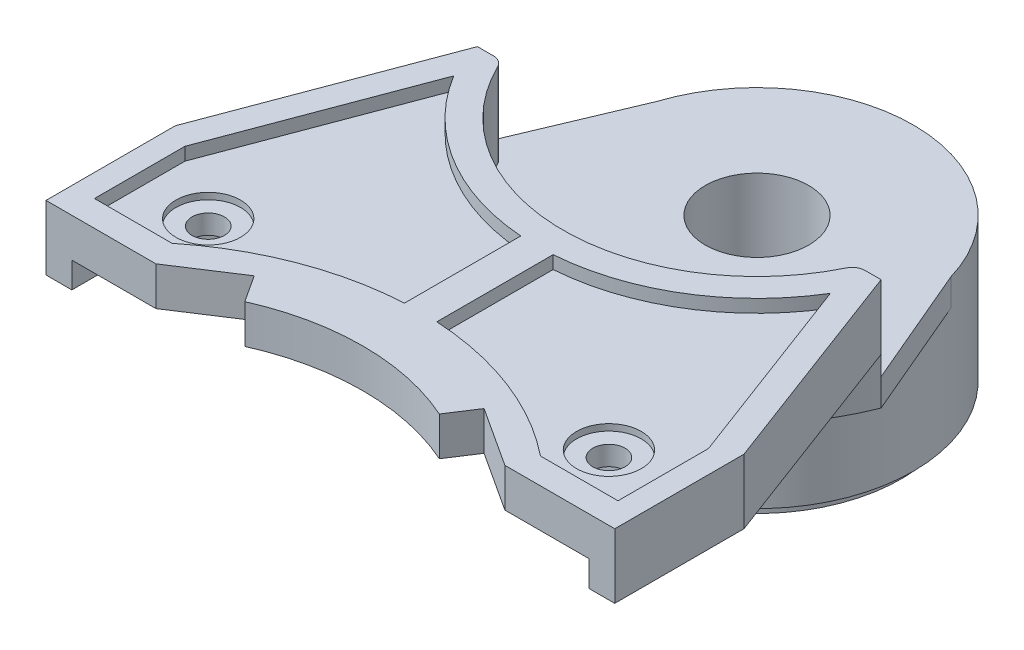
SolidWorks part; units mm, degrees
material "ABS"
ref_plane "Front Plane" through (0, 0, 0) normal (0, 0, 1) x (1, 0, 0)
ref_plane "Top Plane" through (0, 0, 0) normal (0, 1, 0) x (1, 0, 0)
ref_plane "Right Plane" through (0, 0, 0) normal (1, 0, 0) x (0, 0, -1)
sketch "Sketch1" plane through (0, 0, 0) normal (0, 1, 0) x (1, 0, 0)
  line L0 (-22, -33.0049) -> (-13.5, -33.0049)
  line L1 (-13.5, -33.0049) -> (13.5, -33.0049) construction
  line L2 (-22, -33.0049) -> (-22, -23.0049)
  line L3 (0, -30.5) -> (0, 12.5)
  line L4 (-13.5, -33.0049) -> (-8.8902, -30.0049)
  line L5 (0, -2.75) -> (0, 2.75) construction
  line L6 (-8.8902, -30.0049) -> (-7.5266, -32.1003)
  line L7 (-11.7009, 4.3977) -> (-22, -23.0049)
  line L8 (11.7009, 4.3977) -> (22, -23.0049)
  line L9 (8.8902, -30.0049) -> (7.5266, -32.1003)
  line L10 (13.5, -33.0049) -> (8.8902, -30.0049)
  line L11 (22, -33.0049) -> (22, -23.0049)
  line L12 (22, -33.0049) -> (13.5, -33.0049)
  arc A0 (11.7009, 4.3977) -> (-11.7009, 4.3977) centre (0, 0) ccw
  arc A2 (7.5266, -32.1003) -> (-7.5266, -32.1003) centre (0, -49) ccw
  point P5 (0, -33.0049)
  point P11 (0, -49)
  dimension "D1" = 25
  dimension "D5" = 18.5
  dimension "D2" = 8.5
  dimension "D3" = 5.5
  dimension "D4" = 10
  dimension "D6" = 13.5
  dimension "D7" = 2.5
  dimension "D8" = 90
  dimension "D9" = 3
  dimension "D11" = 49
extrude "Boss-Extrude1" add sketch "Sketch1" along normal blind 5 contours A2 L3 A0 L7 L2 L0 L4 L6 | A2 L9 L10 L12 L11 L8 A0 L3
sketch "Sketch3" plane through (0, 5, 0) normal (0, 1, 0) x (1, 0, 0)
  circle A0 centre (0, 0) radius 15
  dimension "D1" = 30
sketch "Sketch6" plane through (0, 5, 0) normal (0, 1, 0) x (1, 0, 0)
  line L0 (1.2511, -26.0226) -> (20.2511, -26.0226) construction
  line L1 (-1.2511, -17.0226) -> (-1.2511, -26.0226)
  line L2 (-1.2511, -26.0226) -> (-20.2511, -26.0226) construction
  line L3 (-20.2511, -24.0049) -> (-20.2511, -31.0049)
  line L4 (-22, -33.0049) -> (-13.5, -33.0049) construction
  line L5 (0, -2.75) -> (0, 2.75) construction
  line L6 (-20.2511, -31.0049) -> (-14.2511, -31.0049)
  line L7 (-20.2511, -24.0049) -> (-14.5704, -8.8904)
  line L8 (-11.7009, 4.3977) -> (-22, -23.0049) construction
  line L9 (20.2511, -24.0049) -> (14.5704, -8.8904)
  line L10 (20.2511, -31.0049) -> (14.2511, -31.0049)
  line L11 (20.2511, -24.0049) -> (20.2511, -31.0049)
  line L12 (1.2511, -17.0226) -> (1.2511, -26.0226)
  arc A0 (-14.5704, -8.8904) -> (-1.2511, -17.0226) centre (0, 0) ccw
  arc A1 (-1.2511, -26.0226) -> (-14.2511, -31.0049) centre (0, -48.7383) ccw
  arc A2 (1.2511, -26.0226) -> (14.2511, -31.0049) centre (0, -48.7383) cw
  arc A3 (14.5704, -8.8904) -> (1.2511, -17.0226) centre (0, 0) cw
  dimension "D10" = 360
  dimension "D8" = 22.7501
  dimension "D2" = 2.5023
  dimension "D3" = 9
  dimension "D4" = 19
  dimension "D5" = 7
  dimension "D6" = 2
  dimension "D7" = 6
sketch "Sketch7" plane through (0, 5, 0) normal (0, 1, 0) x (1, 0, 0)
  circle A0 centre (-15.5, -26.9549) radius 1.25
  circle A1 centre (15.5, -26.9549) radius 1.25
  dimension "D3" = 2.5
  dimension "D4" = 2.5
  dimension "D1" = 31
  dimension "D2" = 26.9549
sketch "Sketch8" plane through (0, 5, 0) normal (0, 1, 0) x (1, 0, 0)
  line L0 (-22, -33.0049) -> (-13.5, -33.0049) construction
  line L1 (0, -2.75) -> (0, 2.75) construction
  circle A0 centre (-15.5, -26.9549) radius 2.5
  circle A1 centre (15.5, -26.9549) radius 2.5
  dimension "D1" = 5
  dimension "D2" = 6.05
  dimension "D3" = 15.5
sketch "Sketch9" plane through (0, 0, 0) normal (0, -1, 0) x (1, 0, 0)
  line L0 (0, 30.5) -> (0, 18) construction
  line L1 (0, -2.75) -> (0, 2.75) construction
  line L2 (22, 33.0049) -> (22, 23.0049) construction
  line L3 (22, 33.0049) -> (13.5, 33.0049) construction
  line L4 (20, 33.0049) -> (20, 27.0049)
  line L5 (-20, 33.0049) -> (-20, 27.0049)
  line L7 (20, 33.0049) -> (-20, 33.0049)
  arc A3 (-20, 27.0049) -> (20, 27.0049) centre (0, 44.7125) ccw
  arc A6 (-7.5266, 32.1003) -> (7.5266, 32.1003) centre (0, 49) ccw construction
  dimension "D5" = 0
  dimension "D2" = 2
  dimension "D1" = 0
  dimension "D6" = 12.5
  dimension "D7" = 0
  dimension "D8" = 44.7125
extrude "Cut-Extrude6" cut sketch "Sketch9" against normal blind 2
sketch "Sketch11" plane through (0, 0, 0) normal (0, -1, 0) x (1, 0, 0)
  line L0 (-20, 33.0049) -> (-20, 23.0049) construction
  line L1 (-20, 23.0049) -> (-10.0731, -3.4072)
  line L2 (-11.7009, -4.3977) -> (-22, 23.0049) construction
  line L3 (-20, 23.0049) -> (-20, 25.5296)
  line L4 (0, -2.75) -> (0, 2.75) construction
  line L5 (20, 23.0049) -> (20, 25.5296)
  line L6 (20, 23.0049) -> (10.0731, -3.4072)
  arc A0 (-20, 25.5296) -> (20, 25.5296) centre (0, 44.7125) ccw
  arc A1 (-10.0731, -3.4072) -> (10.0731, -3.4072) centre (0, 0) ccw
  dimension "D1" = 27.7125
  dimension "D2" = 10
  dimension "D3" = 0
extrude "Cut-Extrude7" cut sketch "Sketch11" against normal blind 2
sketch "Sketch12" plane through (0, 5, 0) normal (0, -1, 0) x (1, 0, 0)
  circle A0 centre (0, 0) radius 16.7324
  dimension "D1" = 33.4649
extrude "Boss-Extrude3" add sketch "Sketch12" along normal blind 8.6
sketch "Sketch13" plane through (0, -3.6, 0) normal (0, -1, 0) x (1, 0, 0)
  circle A0 centre (0, 0) radius 10.4
  circle A1 centre (0, 0) radius 12.1
  dimension "D1" = 20.8
  dimension "D2" = 24.2
sketch "Sketch14" plane through (0, -3.6, 0) normal (0, -1, 0) x (1, 0, 0)
  circle A0 centre (0, 0) radius 6
  dimension "D1" = 12
extrude "Boss-Extrude4" add sketch "Sketch13" along normal blind 10
extrude "Boss-Extrude5" add sketch "Sketch14" along normal blind 10
sketch "Sketch15" plane through (0, -13.6, 0) normal (0, -1, 0) x (1, 0, 0)
  circle A0 centre (0, 0) radius 1.25
  dimension "D1" = 2.5
sketch "Sketch18" plane through (0, -13.6, 0) normal (0, 1, 0) x (1, 0, 0)
extrude "Cut-Extrude10" cut sketch "Sketch6" against normal blind 1
extrude "Cut-Extrude11" cut sketch "Sketch7" against normal through all
extrude "Cut-Extrude12" cut sketch "Sketch8" against normal blind 1.5
extrude "Cut-Extrude14" cut sketch "Sketch3" against normal blind 6.5
sketch "Sketch19" plane through (0, 5, 0) normal (0, 1, 0) x (1, 0, 0)
  line L0 (-15.6142, -6.0143) -> (15.6142, -6.0143)
  arc A0 (15.6142, -6.0143) -> (-15.6142, -6.0143) centre (0, 0) ccw
extrude "Cut-Extrude15" cut sketch "Sketch19" against normal blind 6.5
extrude "Cut-Extrude16" cut sketch "Sketch15" against normal blind 6.5
fillet "Fillet2" radius 1 1 edges at (0, -13.6, -6)
sketch "Sketch20" plane through (0, -13.6, 0) normal (0, -1, 0) x (1, 0, 0)
  circle A0 centre (0, 0) radius 11.15
  circle A1 centre (0, 0) radius 12.5039
  dimension "D1" = 22.3
extrude "Cut-Extrude17" cut sketch "Sketch20" against normal blind 1
sketch "Sketch21" plane through (0, -1.5, 0) normal (0, 1, 0) x (1, 0, 0)
  circle A0 centre (0, 0) radius 4
  dimension "D1" = 8
extrude "Cut-Extrude19" cut sketch "Sketch21" against normal blind 8.8
fillet "Fillet10" radius 1 2 edges at (13.7415, 1.75, 6.0143) (-13.7415, 1.75, 6.0143)
sketch "Sketch22" plane through (0, -3.6, 0) normal (0, -1, 0) x (1, 0, 0)
  line L2 (15.6142, 6.0143) -> (11.6156, -3.3893)
  line L3 (-15.6142, 6.0143) -> (-11.5011, -3.7597)
  arc A0 (-11.5011, -3.7597) -> (11.6156, -3.3893) centre (0, 0) ccw
  arc A1 (-15.6142, 6.0143) -> (15.6142, 6.0143) centre (0, 0) ccw
  arc A2 (-15.6142, 6.0143) -> (15.6142, 6.0143) centre (0, 0) ccw
  circle M3 centre (0, 0) radius 12.1
  circle M4 centre (0, 0) radius 16.7324
  dimension "D2" = 24.2
extrude "Cut-Extrude21" cut sketch "Sketch22" against normal through all contours L3 L2 M4 M3
equation "\"D4@Sketch7\"=\"D3@Sketch7\""
